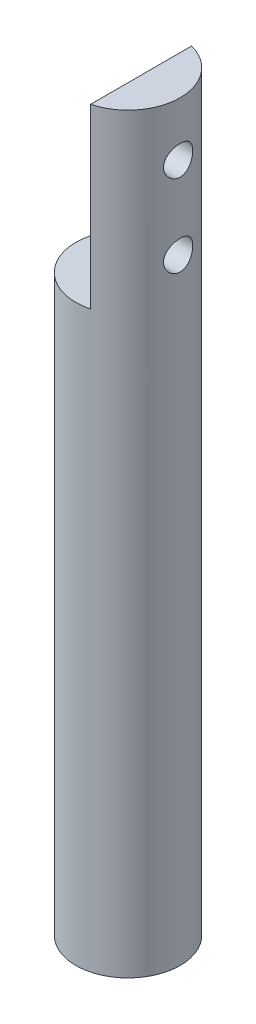
SolidWorks part; units mm, degrees
ref_plane "Front" through (0, 0, 0) normal (0, 0, 1) x (1, 0, 0)
ref_plane "Top" through (0, 0, 0) normal (0, 1, 0) x (1, 0, 0)
ref_plane "Right" through (0, 0, 0) normal (1, 0, 0) x (0, 0, -1)
sketch "草图1" plane through (0, 0, 0) normal (0, 1, 0) x (1, 0, 0)
  circle A0 centre (0, 0) radius 3.175
extrude "凸台-拉伸1" add sketch "草图1" along normal blind 57.15
sketch "草图2" plane through (0, 57.15, 0) normal (0, 1, 0) x (1, 0, 0)
  line L0 (0, 0) -> (0, 3.175) construction
  line L1 (-0.794, 3.175) -> (0.794, 3.175)
  line L2 (0.794, 3.175) -> (0.794, -3.175)
  line L3 (0.794, -3.175) -> (-3.175, -3.175)
  line L4 (-3.175, -3.175) -> (-3.175, 3.175)
  line L5 (-3.175, 3.175) -> (-0.794, 3.175)
  line L6 (0, 0) -> (0.794, 0) construction
  circle A0 centre (0, 0) radius 3.175 construction
  point P8 (0, 3.175)
extrude "切除-拉伸1" cut sketch "草图2" against normal blind 10.795
sketch "草图3" plane through (0.794, 0, 0) normal (-1, 0, 0) x (0, 0, 1)
  line L0 (0, 57.15) -> (0, 53.855) construction
  line L1 (3.0741, 57.15) -> (-3.0741, 57.15) construction
  line L2 (0, 57.15) -> (0, 48.855) construction
  line L3 (0, 53.855) -> (0, 57.15) construction
  circle A0 centre (0, 53.855) radius 0.889
  circle A1 centre (0, 48.855) radius 0.889
extrude "切除-拉伸2" cut sketch "草图3" against normal blind 10.795
sketch "草图4" plane through (0, 0, 0) normal (0, -1, 0) x (1, 0, 0)
  line L0 (0, 0) -> (-3.175, 0) construction
  line L1 (-3.175, 0) -> (0, 0) construction
  line L2 (0, 0) -> (0, -3.175) construction
  line L3 (0, -3.175) -> (0, -1.5875) construction
  line L4 (0, -1.5875) -> (0, -2.3813) construction
  line L5 (0, -2.3813) -> (-1.9811, -2.3813) construction
  line L6 (-1.9811, -2.3813) -> (1.9451, -2.3813) construction
  line L7 (-1.9811, -2.3813) -> (1.9451, -2.3813)
  line L8 (1.9451, -2.3813) -> (1.9451, -3.175)
  line L9 (1.9451, -3.175) -> (-1.9811, -3.175)
  line L10 (-1.9811, -3.175) -> (-1.9811, -2.3813)
  circle A0 centre (0, 0) radius 3.175 construction
extrude "切除-拉伸3" cut sketch "草图4" against normal blind 8.573
sketch "草图5" plane through (0, 0, 0) normal (0, -1, 0) x (1, 0, 0)
  circle A0 centre (0, 0) radius 3.7749
extrude "切除-拉伸4" cut sketch "草图5" against normal blind 11.4
